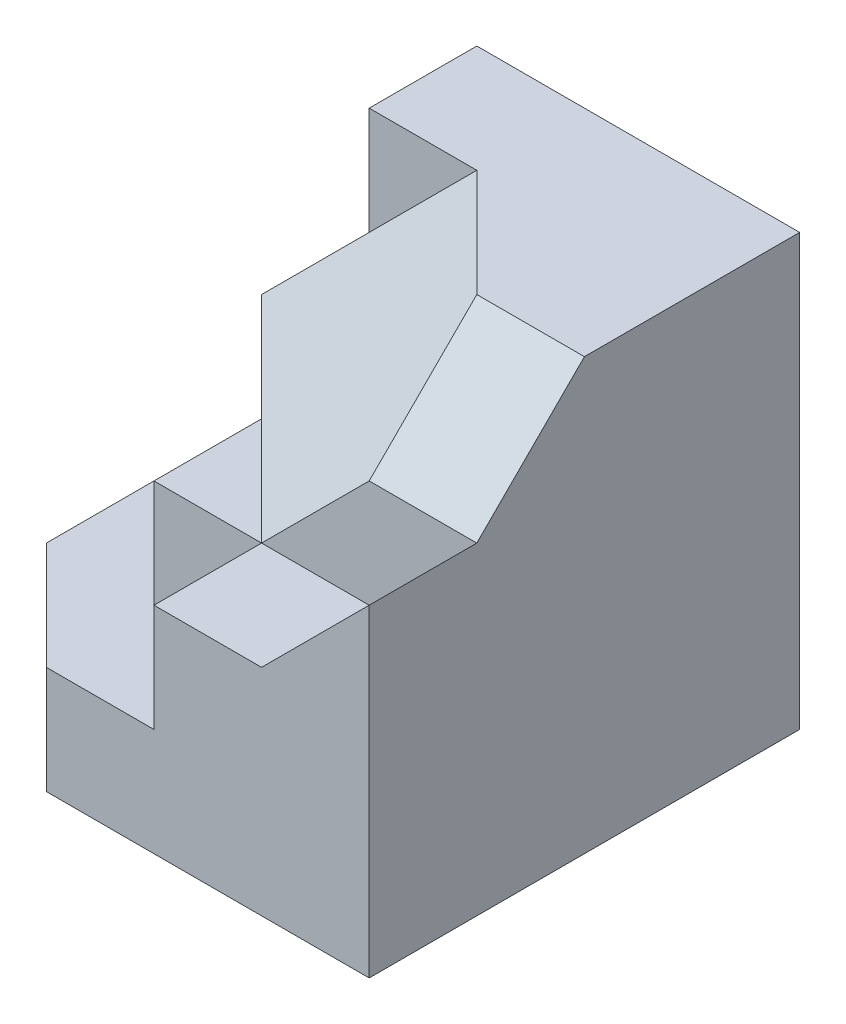
SolidWorks part; units mm, degrees
ref_plane "Front Plane" through (0, 0, 0) normal (0, 0, 1) x (1, 0, 0)
ref_plane "Top Plane" through (0, 0, 0) normal (0, 1, 0) x (1, 0, 0)
ref_plane "Right Plane" through (0, 0, 0) normal (1, 0, 0) x (0, 0, -1)
sketch "Sketch1" plane through (0, 0, 0) normal (0, 1, 0) x (1, 0, 0)
  line L0 (-23.7915, 10) -> (-8.7915, 10)
  line L1 (-8.7915, 10) -> (-8.7915, 0)
  line L2 (-8.7915, 0) -> (-13.7915, 0)
  line L3 (-13.7915, 0) -> (-18.7915, 5)
  line L4 (-18.7915, 5) -> (-23.7915, 5)
  line L5 (-23.7915, 5) -> (-23.7915, 10)
  dimension "D1" = 15
  dimension "D2" = 10
  dimension "D3" = 5
  dimension "D4" = 5
  dimension "D5" = 5
extrude "Boss-Extrude1" add sketch "Sketch1" along normal blind 20
sketch "Sketch2" plane through (0, 0, 0) normal (0, 0, 1) x (1, 0, 0)
  line L1 (-13.7915, 0) -> (-8.7915, 0)
  line L2 (-13.7915, 0) -> (-13.7915, 20)
  line L3 (-13.7915, 20) -> (-8.7915, 20)
  line L4 (-8.7915, 0) -> (-8.7915, 20)
extrude "Boss-Extrude2" add sketch "Sketch2" along normal blind 5
sketch "Sketch3" plane through (-13.7915, 0, 0) normal (-1, 0, 0) x (0, 0, 1)
  line L0 (0, 20) -> (5, 15)
  line L1 (5, 20) -> (5, 0) construction
  line L2 (5, 15) -> (5, 20)
  line L3 (5, 20) -> (0, 20)
  dimension "D1" = 5
extrude "Cut-Extrude1" cut sketch "Sketch3" against normal blind 5
sketch "Sketch4" plane through (-23.7915, 0, 0) normal (-1, 0, 0) x (0, 0, 1)
  line L1 (-10, 0) -> (-5, 0)
  line L2 (-10, 0) -> (-10, 15)
  line L3 (-10, 15) -> (-5, 15)
  line L4 (-5, 0) -> (-5, 15)
  dimension "D1" = 15
extrude "Boss-Extrude4" add sketch "Sketch4" along normal blind 5
sketch "Sketch6" plane through (0, 0, -5) normal (0, 0, 1) x (1, 0, 0)
  line L0 (-23.7915, 15) -> (-28.7915, 15)
  line L1 (-28.7915, 15) -> (-28.7915, 10)
  line L2 (-28.7915, 0) -> (-28.7915, 15) construction
  line L3 (-28.7915, 10) -> (-23.7915, 15)
  dimension "D1" = 5
extrude "Cut-Extrude3" cut sketch "Sketch6" against normal blind 5
sketch "Sketch7" plane through (0, 0, 5) normal (0, 0, 1) x (1, 0, 0)
  line L1 (-13.7915, 0) -> (-8.7915, 0)
  line L2 (-13.7915, 0) -> (-13.7915, 15)
  line L3 (-13.7915, 15) -> (-8.7915, 15)
  line L4 (-8.7915, 0) -> (-8.7915, 15)
extrude "Boss-Extrude5" add sketch "Sketch7" along normal blind 5
sketch "Sketch8" plane through (0, 0, 10) normal (0, 0, 1) x (1, 0, 0)
  line L0 (-8.7915, 15) -> (-13.7915, 15)
  line L1 (-13.7915, 15) -> (-13.7915, 10)
  line L2 (-13.7915, 20) -> (-13.7915, 0) construction
  line L3 (-13.7915, 10) -> (-8.7915, 15)
  dimension "D1" = 5
extrude "Cut-Extrude4" cut sketch "Sketch8" against normal blind 5
ref_plane "Plane1" through (0, 0, 0) normal (0, -1, 0) x (-1, 0, 0)
sketch "Sketch9" plane through (0, 0, 0) normal (0, -1, 0) x (-1, 0, 0)
  line L0 (28.7915, 5) -> (18.7915, 5)
  line L1 (18.7915, 5) -> (13.7915, 0)
  line L2 (13.7915, 0) -> (13.7915, -5)
  line L3 (13.7915, -10) -> (13.7915, 0) construction
  line L4 (13.7915, -5) -> (18.7915, -5)
  line L5 (18.7915, -5) -> (28.7915, 5)
  dimension "D1" = 5
  dimension "D2" = 5
extrude "Boss-Extrude6" add sketch "Sketch9" against normal blind 20
sketch3d "3DSketch1"
  line L0 (-18.7915, 20, 5) -> (-18.7915, 0, 5) construction
  line L1 (-8.7915, 20, -10) -> (-23.7915, 20, -10) construction
  line L2 (-23.7915, 20, -10) -> (-23.7915, 20, -5) construction
  line L3 (-18.7915, 20, 5) -> (-28.7915, 20, -5) construction
  line L4 (-28.7915, 10, -5) -> (-18.7915, 20, -5)
  line L5 (-18.7915, 20, -5) -> (-13.7915, 20, 0)
  line L6 (-13.7915, 20, 0) -> (-13.7915, 15, 5)
  line L7 (-13.7915, 15, 5) -> (-18.7915, 10, 5)
  line L8 (-18.7915, 10, 5) -> (-28.7915, 10, -5)
  point P0 (-18.7915, 20, -5)
  point P2 (-28.7915, 10, -5)
  point P4 (-18.7915, 10, 5)
  point P6 (-13.7915, 15, 5)
  point P9 (-13.7915, 20, 0)
  dimension "D1" = 5
  dimension "D2" = 5
  dimension "D3" = 10
extrude "Cut-Extrude15" cut sketch "3DSketch1" along direction (0, -1, 0) on the side of the normal blind 61
sketch "Sketch10" plane through (0, 0, 0) normal (0, -1, 0) x (-1, 0, 0)
  line L0 (28.7915, 5) -> (18.7915, -5)
  line L1 (18.7915, -5) -> (13.7915, -5)
  line L2 (13.7915, -5) -> (13.7915, -10)
  line L3 (13.7915, -10) -> (23.7915, -10)
  line L4 (23.7915, -10) -> (28.7915, -5)
  line L5 (28.7915, -5) -> (28.7915, 5)
  dimension "D1" = 10
extrude "Boss-Extrude7" add sketch "Sketch10" against normal blind 5
sketch "Sketch11" plane through (0, 5, 0) normal (0, 1, 0) x (1, 0, 0)
  line L0 (-18.7915, -5) -> (-13.7915, -5)
  line L1 (-13.7915, -5) -> (-13.7915, -10)
  line L2 (-13.7915, -10) -> (-18.7915, -10)
  line L3 (-13.7915, -10) -> (-23.7915, -10) construction
  line L4 (-18.7915, -10) -> (-18.7915, -5)
  line L5 (-23.7915, 0) -> (-18.7915, -5)
  line L6 (-28.7915, 5) -> (-18.7915, -5) construction
  line L7 (-23.7915, -5) -> (-23.7915, 0)
  line L8 (-23.7915, -5) -> (-18.7915, -5)
  line M3 (-23.7915, -10) -> (-13.7915, -10)
  line M4 (-13.7915, -10) -> (-13.7915, -5)
  line M5 (-13.7915, -5) -> (-18.7915, -5)
  line M6 (-18.7915, -5) -> (-28.7915, 5)
  dimension "D1" = 5
extrude "Boss-Extrude8" add sketch "Sketch11" along normal blind 5 contours L4 M3 M4 M5 | L7 L8 M6
